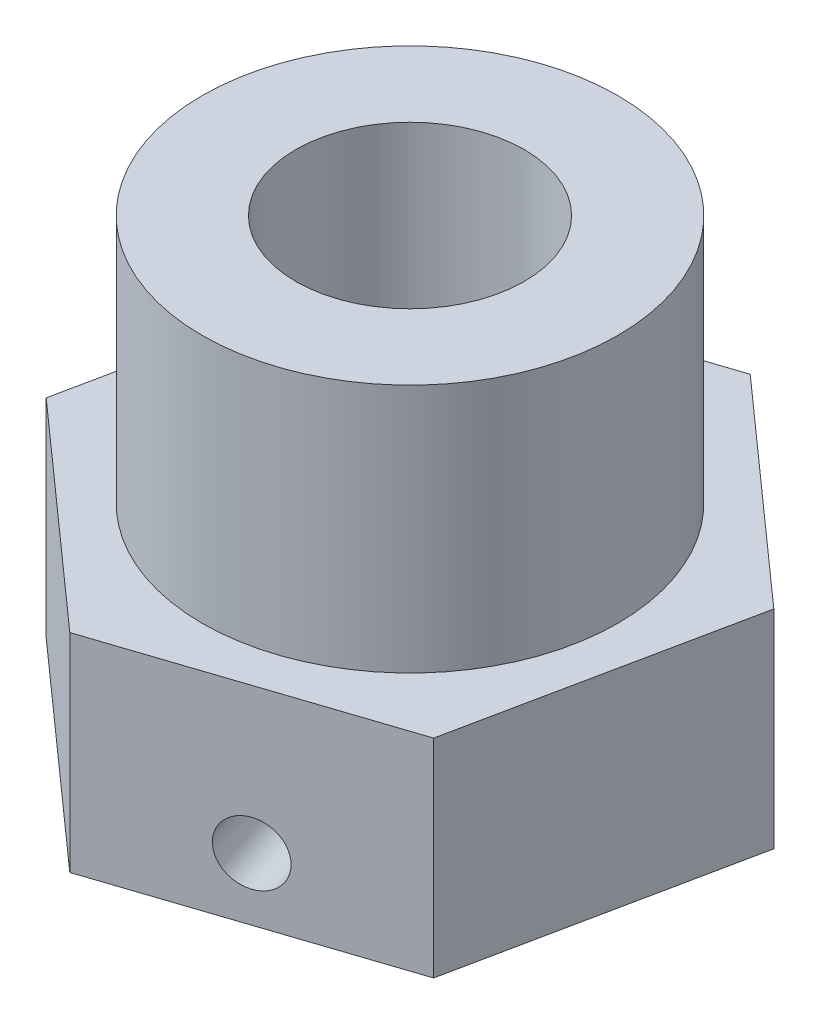
SolidWorks part; units mm, degrees
ref_plane "Alzado" through (0, 0, 0) normal (0, 0, 1) x (1, 0, 0)
ref_plane "Planta" through (0, 0, 0) normal (0, 1, 0) x (1, 0, 0)
ref_plane "Vista lateral" through (0, 0, 0) normal (1, 0, 0) x (0, 0, -1)
sketch "Croquis1" plane through (0, 0, 0) normal (0, 1, 0) x (1, 0, 0)
  line L1 (1.4017, 6.7849) -> (-5.1751, 4.6064)
  line L2 (-5.1751, 4.6064) -> (-6.5768, -2.1786)
  line L3 (-6.5768, -2.1786) -> (-1.4017, -6.7849)
  line L4 (-1.4017, -6.7849) -> (5.1751, -4.6064)
  line L5 (5.1751, -4.6064) -> (6.5768, 2.1786)
  line L6 (6.5768, 2.1786) -> (1.4017, 6.7849)
  circle A0 centre (0, 0) radius 6 construction
  circle A1 centre (0, 0) radius 2.75
  dimension "D1" = 5.5
  dimension "D2" = 12
extrude "Saliente-Extruir1" add sketch "Croquis1" along normal blind 5
sketch "Croquis3" plane through (0, 5, 0) normal (0, 1, 0) x (1, 0, 0)
  circle A0 centre (0, 0) radius 5
  circle A1 centre (0, 0) radius 2.75
  dimension "D1" = 10
  dimension "D2" = 5.5
extrude "Saliente-Extruir2" add sketch "Croquis3" along normal blind 6
sketch "Croquis2" plane through (1.8867, 0, 5.6957) normal (0.3144, 0, 0.9493) x (0.9493, 0, -0.3144)
  line L0 (-3.4641, 0) -> (3.4641, 0) construction
  circle A0 centre (0, 1.5) radius 0.75
  dimension "D2" = 1.5
  dimension "D1" = 1.5
extrude "Cortar-Extruir1" cut sketch "Croquis2" against normal through all
